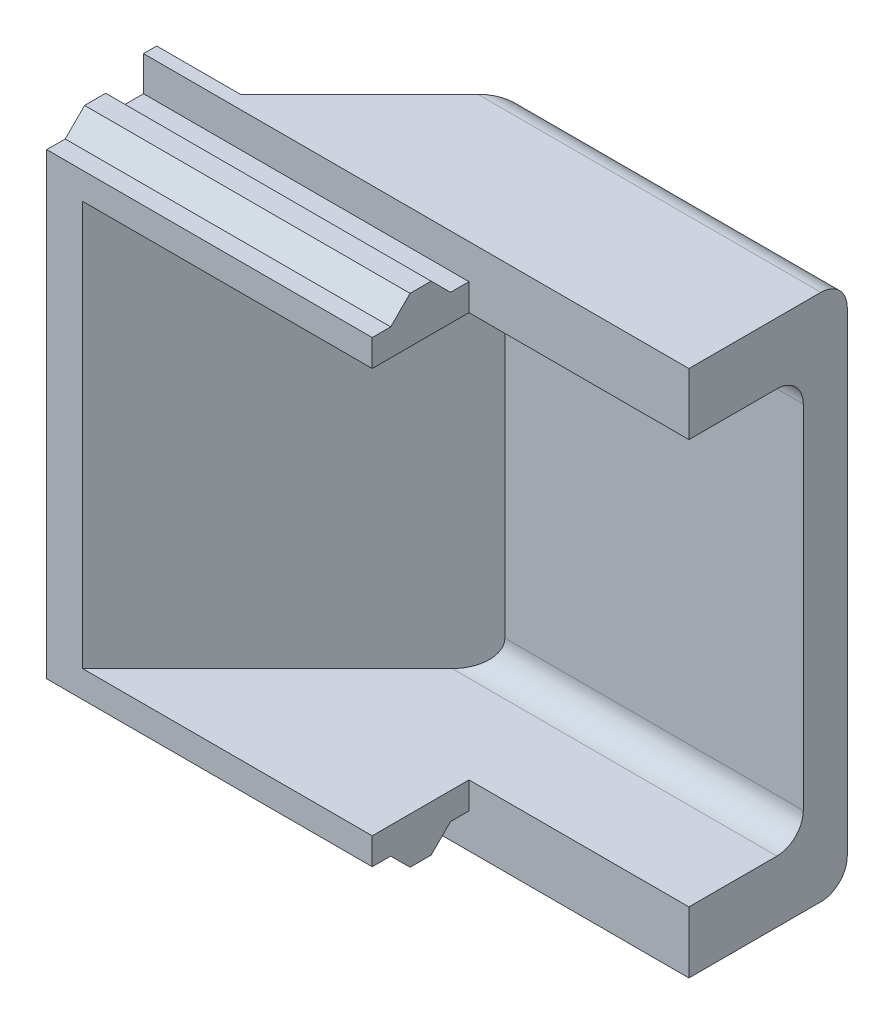
SolidWorks part; units mm, degrees
ref_plane "Front" through (0, 0, 0) normal (0, 0, 1) x (1, 0, 0)
ref_plane "Top" through (0, 0, 0) normal (0, 1, 0) x (1, 0, 0)
ref_plane "Right" through (0, 0, 0) normal (1, 0, 0) x (0, 0, -1)
sketch "Sketch1" plane through (0, 0, 0) normal (0, 1, 0) x (1, 0, 0)
  line L0 (0, 0) -> (0, 3.175)
  line L1 (0, 3.175) -> (2.413, 3.175)
  line L2 (2.413, 3.175) -> (6.604, 7.366)
  line L3 (6.604, 7.366) -> (15.748, 7.366)
  line L4 (15.748, 7.366) -> (15.748, 2.794)
  line L5 (15.748, 2.794) -> (9.398, 2.794)
  line L6 (9.398, 2.794) -> (9.398, 0)
  line L7 (9.398, 0) -> (0, 0)
  point P5 (7.62, 7.366)
  point P6 (5.842, 7.366)
  point P10 (7.1755, 0)
  point P11 (7.1755, 11.221)
  point P12 (6.6167, 0)
  point P13 (6.6167, 11.221)
  point P29 (7.1755, 6.2738)
  point P30 (4.2252, 6.2738)
  point P31 (7.1755, 5.6642)
  point P32 (4.2252, 5.6642)
  point P33 (7.1755, 6.8834)
  point P34 (4.2252, 6.8834)
  point P35 (7.1755, 5.0546)
  point P36 (4.2252, 5.0546)
  dimension "D1" = 9.398
  dimension "D2" = 6.35
  dimension "D3" = 3.175
  dimension "D4" = 15.748
  dimension "D8" = 7.366
  dimension "D5" = 9.144
  dimension "D6" = 225
  dimension "D7" = 2.794
extrude "Boss-Extrude1" add sketch "Sketch1" against normal blind 15.24
sketch "Sketch5" plane through (0, 0, 0) normal (-1, 0, 0) x (0, 0, 1)
  line L0 (-3.175, -7.62) -> (2.3778, -7.62) construction
  line L1 (-3.175, -15.24) -> (-3.175, 0) construction
  line L2 (0, -1.0033) -> (0, 0)
  line L3 (-1.0922, -0.4445) -> (-1.7018, -0.4445)
  line L4 (0, 0) -> (-2.794, 0)
  line L5 (-2.794, 0) -> (-2.794, -1.0033)
  line L6 (-2.794, -1.0033) -> (-2.2606, -1.0033)
  line L7 (0, -15.24) -> (0, 0) construction
  line L8 (-2.794, 0) -> (0, 0) construction
  line L9 (-3.175, -3.2997) -> (0, -3.2997) construction
  line L10 (-1.397, -0.4445) -> (-1.397, -1.6208) construction
  line L11 (-0.5334, -1.0033) -> (0, -1.0033)
  line L17 (-0.5334, -1.0033) -> (-1.0922, -0.4445)
  line L18 (-1.7018, -0.4445) -> (-2.2606, -1.0033)
  point P6 (-3.175, -1.0033)
  point P7 (2.3778, -1.0033)
  point P10 (-3.175, -0.4445)
  point P11 (2.3778, -0.4445)
  point P28 (-0.4826, 5.25)
  point P30 (-2.3114, 5.25)
  dimension "D5" = 0.6096
  dimension "D6" = 1.397
  dimension "D1" = 90
  dimension "D2" = 6.6167
  dimension "D3" = 7.1755
  dimension "D4" = 2.794
extrude "Cut-Extrude1" cut sketch "Sketch5" against normal through all
ref_plane "Plane1" through (0, -7.62, 0) normal (0, 1, 0) x (1, 0, 0)
mirror "Mirror1" about plane through (0, -7.62, 0) normal (0, 1, 0) of "Cut-Extrude1"
sketch "Sketch6" plane through (0, -7.62, 0) normal (0, 1, 0) x (1, 0, 0)
  line L0 (15.748, 6.096) -> (7.1301, 6.096)
  line L1 (15.748, 7.366) -> (15.748, 2.794) construction
  line L2 (7.1301, 6.096) -> (1.0341, 0)
  line L6 (1.0341, 0) -> (15.748, 0)
  line L7 (15.748, 0) -> (15.748, 6.096)
  line L8 (6.604, 7.366) -> (15.748, 7.366) construction
  line L9 (2.413, 3.175) -> (6.604, 7.366) construction
  dimension "D1" = 1.27
  dimension "D2" = 1.27
extrude "Cut-Extrude2" cut sketch "Sketch6" against normal mid plane 11.684
fillet "Fillet1" radius 0.762 4 edges at (11.439, -1.778, -6.096) (11.439, -13.462, -6.096) (11.176, -15.24, -7.366) (11.176, 0, -7.366)
